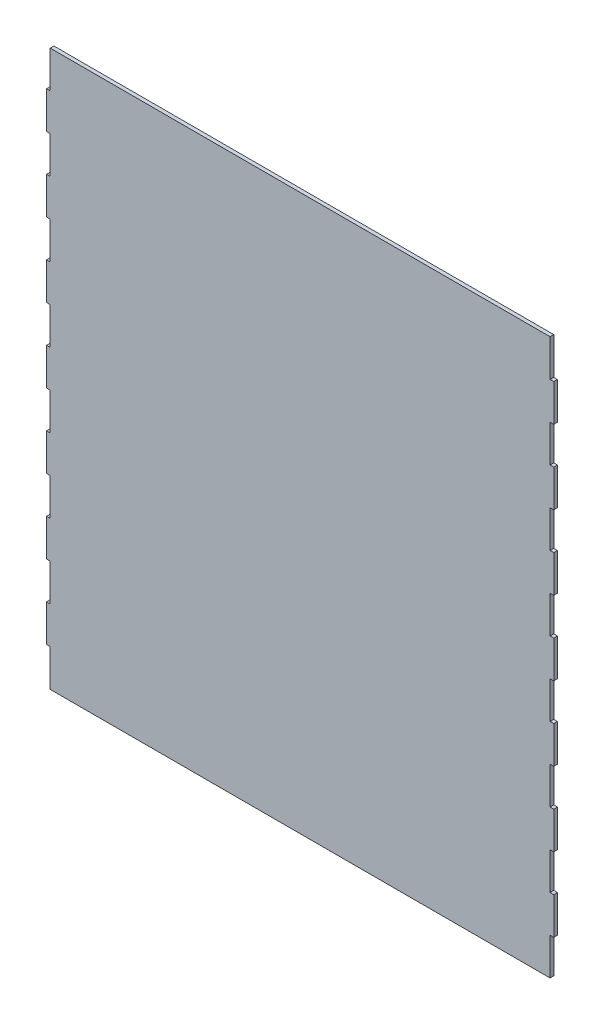
SolidWorks part; units mm, degrees
ref_plane "Front Plane" through (0, 0, 0) normal (0, 0, 1) x (1, 0, 0)
ref_plane "Top Plane" through (0, 0, 0) normal (0, 1, 0) x (1, 0, 0)
ref_plane "Right Plane" through (0, 0, 0) normal (1, 0, 0) x (0, 0, -1)
sketch "Sketch1" plane through (0, 0, 0) normal (0, 0, 1) x (1, 0, 0)
  line L1 (-161.6893, 107.8431) -> (112.3107, 107.8431)
  line L2 (-161.6893, 107.8431) -> (-161.6893, -192.1569)
  line L3 (-161.6893, -192.1569) -> (112.3107, -192.1569)
  line L4 (112.3107, 107.8431) -> (112.3107, -192.1569)
  dimension "D1" = 300
  dimension "D2" = 274
extrude "Boss-Extrude1" add sketch "Sketch1" along normal blind 2
sketch "Sketch2" plane through (0, 0, 2) normal (0, 0, 1) x (1, 0, 0)
  line L1 (-161.6893, 107.8431) -> (-159.6893, 107.8431)
  line L2 (-161.6893, 107.8431) -> (-161.6893, 87.8431)
  line L3 (-161.6893, 87.8431) -> (-159.6893, 87.8431)
  line L4 (-159.6893, 107.8431) -> (-159.6893, 87.8431)
  dimension "D1" = 2
  dimension "D2" = 20
extrude "Cut-Extrude1" cut sketch "Sketch2" against normal blind 4
pattern_linear "LPattern1" count 8 spacing 40 along (0, -1, 0) of "Cut-Extrude1"
sketch "Sketch4" plane through (0, 0, 2) normal (0, 0, 1) x (1, 0, 0)
  line L0 (-24.6893, 95.2773) -> (-24.6893, 5.5343)
  line L1 (112.3107, -192.1569) -> (112.3107, 107.8431) construction
  line L2 (-161.6893, 87.8431) -> (-161.6893, 67.8431) construction
  dimension "D1" = 137
  dimension "D2" = 137
  dimension "D3" = 137
ref_plane "Plane1" through (-24.6893, 0, 0) normal (-1, 0, 0) x (0, -1, 0)
mirror "Mirror1" about plane through (-24.6893, 0, 0) normal (-1, 0, 0) of "LPattern1", "Cut-Extrude1"
